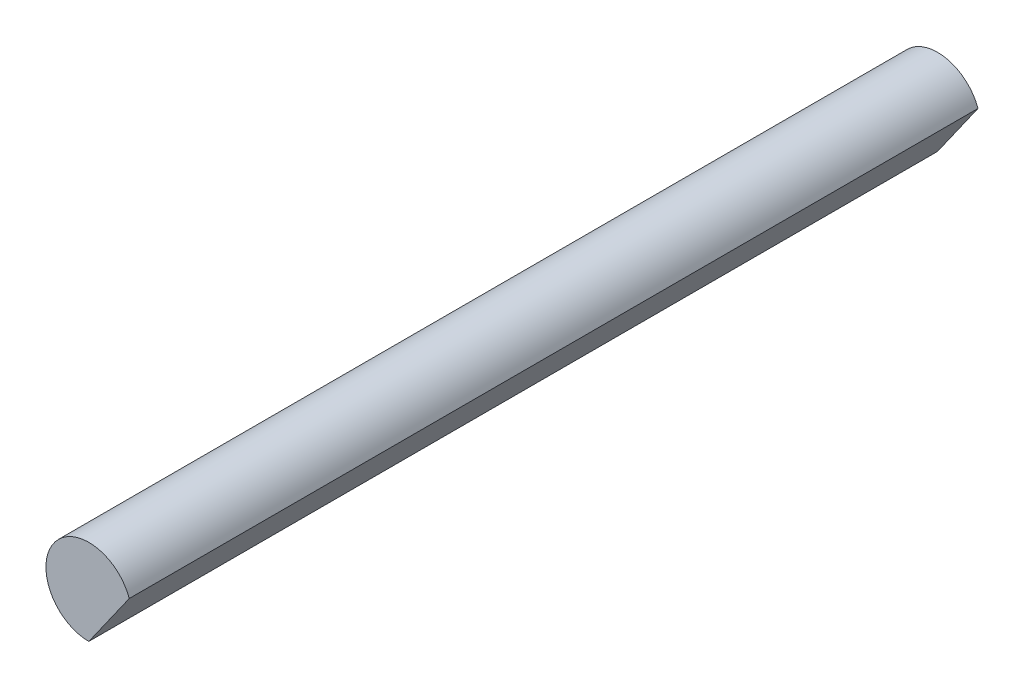
SolidWorks part; units mm, degrees
material "ABS"
ref_plane "Front Plane" through (0, 0, 0) normal (0, 0, 1) x (1, 0, 0)
ref_plane "Top Plane" through (0, 0, 0) normal (0, 1, 0) x (1, 0, 0)
ref_plane "Right Plane" through (0, 0, 0) normal (1, 0, 0) x (0, 0, -1)
sketch "Sketch1" plane through (0, 0, 0) normal (0, 0, 1) x (1, 0, 0)
  line L2 (-0.0017, -1.5) -> (1.4119, 0.5065)
  arc A2 (1.4119, 0.5065) -> (-0.0017, -1.5) centre (0, 0) ccw
extrude "Boss-Extrude1" add sketch "Sketch1" along normal up to surface (29.66 mm away)
